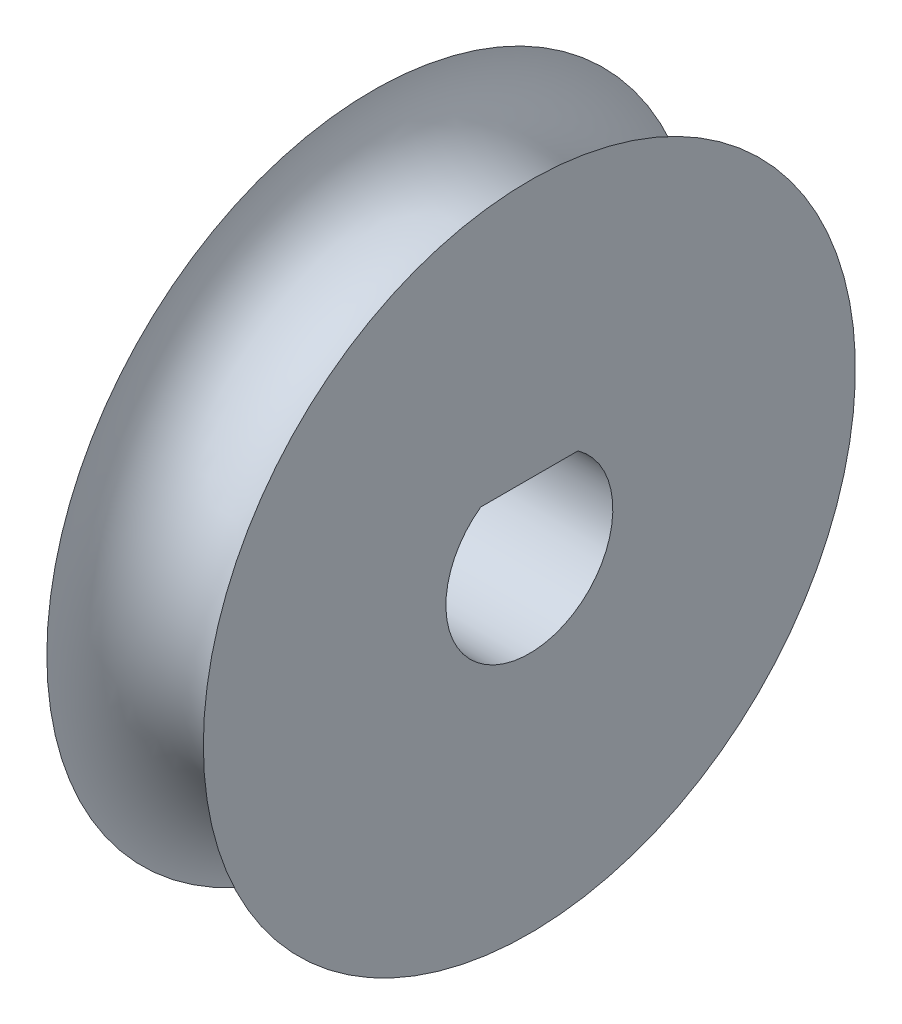
SolidWorks part; units mm, degrees
ref_plane "Front Plane" through (0, 0, 0) normal (0, 0, 1) x (1, 0, 0)
ref_plane "Top Plane" through (0, 0, 0) normal (0, 1, 0) x (1, 0, 0)
ref_plane "Right Plane" through (0, 0, 0) normal (1, 0, 0) x (0, 0, -1)
sketch "Sketch1" plane through (0, 0, 0) normal (0, 0, 1) x (1, 0, 0)
  line L0 (0, 0) -> (0, 12.065) construction
  line L1 (0, 0) -> (0, 12.065) construction
  line L3 (-3.81, 15.875) -> (-3.81, 0)
  line L4 (-3.81, 0) -> (3.81, 0)
  line L5 (3.81, 15.875) -> (3.81, 0)
  line L6 (-1.0783, 12.2208) -> (3.81, 0) construction
  line L7 (-3.81, 0) -> (3.81, 19.05) construction
  line L8 (0, 19.05) -> (0, 12.065) construction
  arc A0 (-3.81, 15.875) -> (3.81, 15.875) centre (0, 15.875) ccw
  point P3 (0, 9.525)
  point P11 (0, 0)
  dimension "D1" = 19.05
  dimension "D2" = 7.62
revolve "Revolve1" add sketch "Sketch1" angle 360 about L4
sketch "Sketch2" plane through (3.81, 0, 0) normal (1, 0, 0) x (0, 0, -1)
  line L0 (0, 4.064) -> (0, 3.302) construction
  line L1 (-2.3692, 3.302) -> (2.3692, 3.302)
  arc A0 (-2.3692, 3.302) -> (2.3692, 3.302) centre (0, 0) ccw
  point P8 (0, 3.302)
  dimension "D1" = 8.128
extrude "Cut-Extrude1" cut sketch "Sketch2" against normal through all
